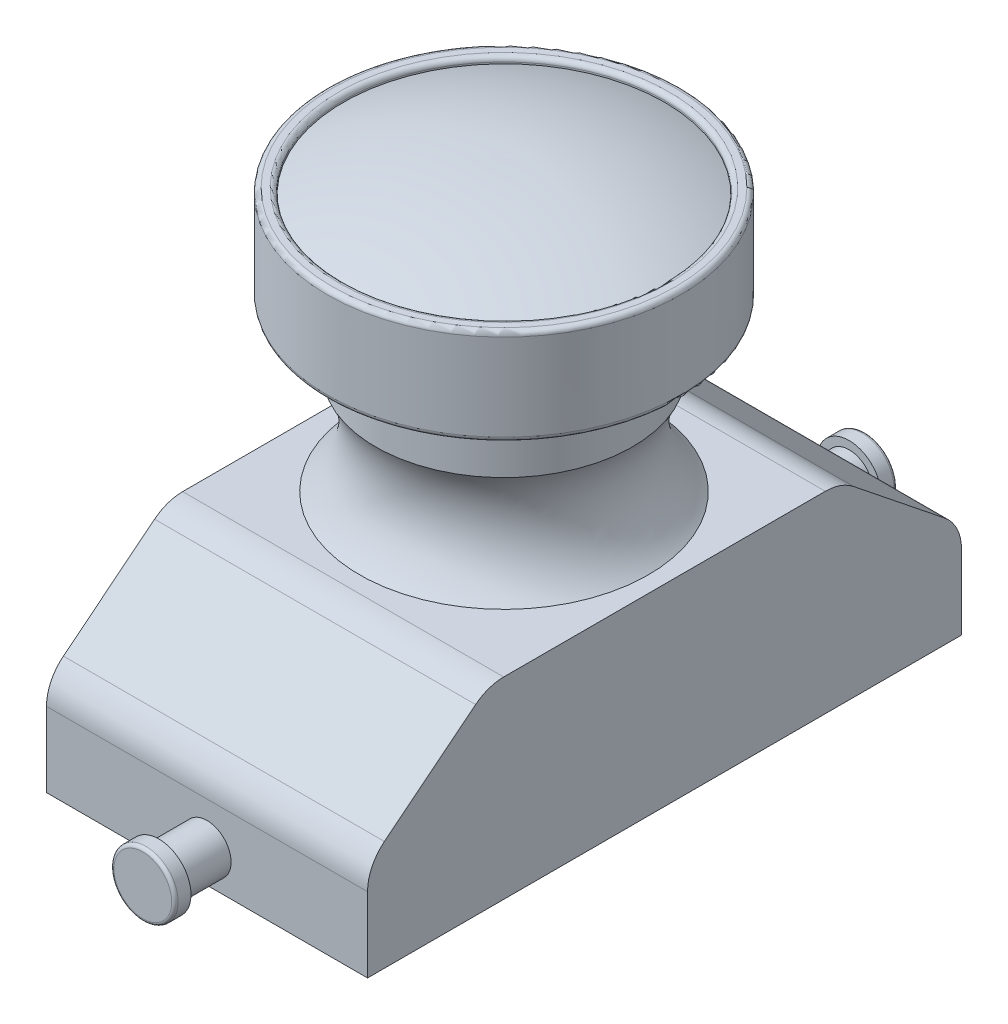
SolidWorks part; units mm, degrees
ref_plane "Front Plane" through (0, 0, 0) normal (0, 0, 1) x (1, 0, 0)
ref_plane "Top Plane" through (0, 0, 0) normal (0, 1, 0) x (1, 0, 0)
ref_plane "Right Plane" through (0, 0, 0) normal (1, 0, 0) x (0, 0, -1)
sketch "Sketch1" plane through (0, 0, 0) normal (1, 0, 0) x (0, 0, -1)
  line L0 (0, 0) -> (0, 6) construction
  line L1 (9.25, 3) -> (5.5, 6)
  line L2 (-9.25, 3) -> (-9.25, 0)
  line L3 (-9.25, 0) -> (9.25, 0)
  line L4 (9.25, 3) -> (9.25, 0)
  line L5 (-9.25, 3) -> (-5.5, 6)
  line L6 (-5.5, 6) -> (5.5, 6)
  dimension "D1" = 18.5
  dimension "D2" = 3
  dimension "D3" = 3
  dimension "D4" = 11
extrude "Boss-Extrude1" add sketch "Sketch1" along normal mid plane 10
sketch "Sketch2" plane through (0, 0, 0) normal (1, 0, 0) x (0, 0, -1)
  line L0 (0, 0) -> (0, 6) construction
  line L1 (5.5, 6) -> (-5.5, 6) construction
  line L2 (0, 6) -> (0, 14)
  line L3 (0, 14) -> (5, 14)
  line L4 (5, 14) -> (5, 14.2)
  line L5 (5, 14.2) -> (5.5, 14.2)
  line L6 (5.5, 14.2) -> (5.5, 11.2)
  line L7 (5.5, 11.2) -> (4, 11.2)
  line L8 (4, 11.2) -> (4, 9.2)
  line L9 (0, 6) -> (4.5, 6)
  arc A0 (4, 9.2) -> (4.5, 6) centre (6.1318, 7.894) ccw
  dimension "D3" = 2.5
  dimension "D1" = 8
  dimension "D2" = 4.5
  dimension "D4" = 2
  dimension "D5" = 1.5
  dimension "D6" = 5
  dimension "D7" = 3
  dimension "D8" = 0.2
  dimension "D9" = 0.5
revolve "Revolve1" add sketch "Sketch2" angle 360 about L0
sketch "Sketch3" plane through (0, 0, 0) normal (1, 0, 0) x (0, 0, -1)
  line L0 (0, 14.2) -> (0, 15)
  line L1 (5, 14.2) -> (-5, 14.2) construction
  line L2 (0, 14.2) -> (0, 14)
  line L3 (0, 14) -> (-5, 14)
  arc A0 (-5, 14) -> (0, 15) centre (-0.2003, 3.0017) cw
  dimension "D4" = 12
  dimension "D1" = 0.8
  dimension "D2" = 0.2
  dimension "D3" = 5
revolve "Revolve2" add sketch "Sketch3" angle 360 about L2
fillet "Fillet1" radius 0.15 3 edges at (0, 11.2, -5.5) (0, 14.2, -5.5) (0, 14.2, -5)
fillet "Fillet2" radius 1.4 4 edges at (0, 3, 9.25) (0, 6, 5.5) (0, 3, -9.25) (0, 6, -5.5)
sketch "Sketch4" plane through (0, 0, -9.25) normal (0, 0, -1) x (-1, 0, 0)
  circle A0 centre (0, 1) radius 0.75
  dimension "D1" = 1.5
  dimension "D2" = 1
extrude "Boss-Extrude2" add sketch "Sketch4" along normal blind 2
mirror "Mirror1" about plane through (0, 0, 0) normal (0, 0, 1) of "Boss-Extrude2"
sketch "Sketch5" plane through (0, 0, 11.25) normal (0, 0, 1) x (1, 0, 0)
  circle A0 centre (0, 1) radius 1
  circle A1 centre (0, 1) radius 0.75 construction
  dimension "D1" = 2
extrude "Boss-Extrude3" add sketch "Sketch5" against normal blind 0.5
fillet "Fillet3" radius 0.1 1 edges at (1, 1, 11.25)
mirror "Mirror2" about plane through (0, 0, 0) normal (0, 0, 1) of "Boss-Extrude3", "Fillet3"
